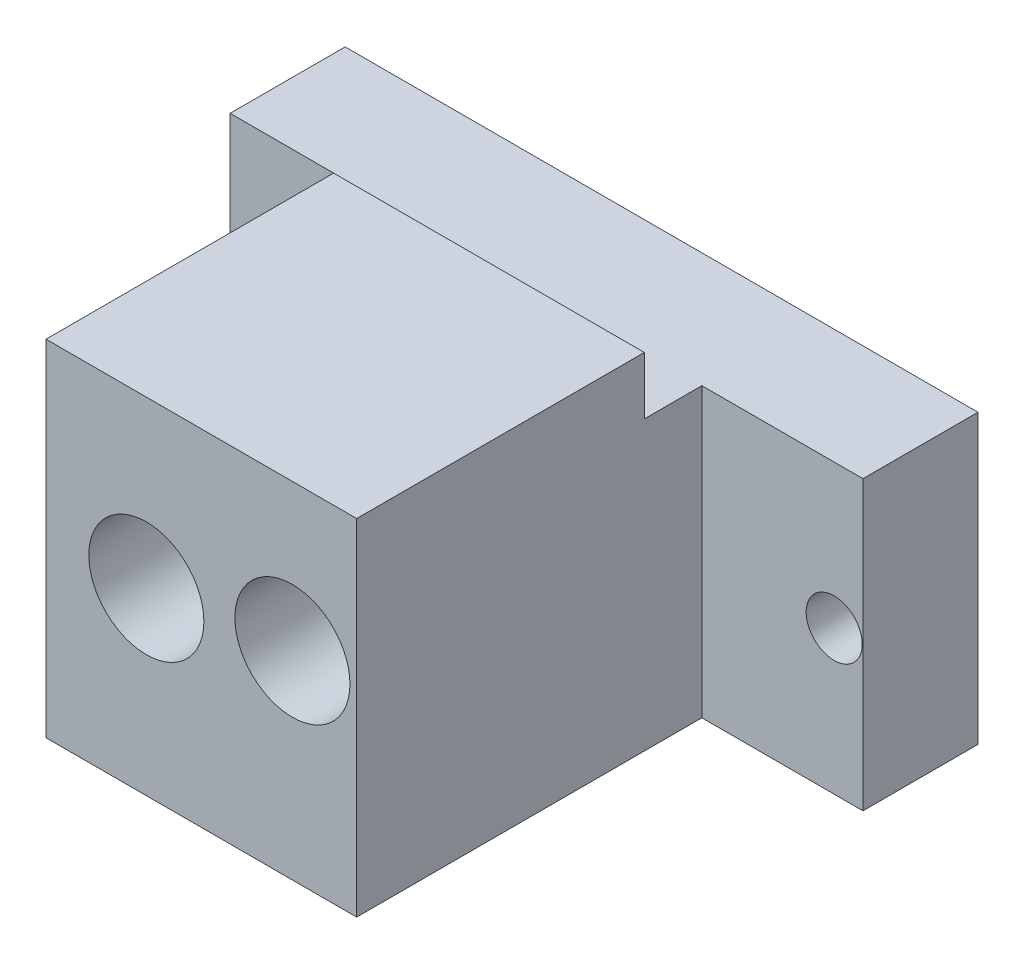
SolidWorks part; units mm, degrees
ref_plane "Front Plane" through (0, 0, 0) normal (0, 0, 1) x (1, 0, 0)
ref_plane "Top Plane" through (0, 0, 0) normal (0, 1, 0) x (1, 0, 0)
ref_plane "Right Plane" through (0, 0, 0) normal (1, 0, 0) x (0, 0, -1)
sketch "Sketch1" plane through (0, 0, 0) normal (0, 0, 1) x (1, 0, 0)
  line L0 (27.5, 25) -> (27.5, 4.2208) construction
  line L1 (0, 0) -> (55, 0)
  line L2 (0, 0) -> (0, 25)
  line L3 (0, 25) -> (55, 25)
  line L4 (55, 0) -> (55, 25)
  circle A0 centre (52.5, 12.5) radius 2.4351
  circle A1 centre (2.5, 12.5) radius 2.4351
  point P7 (27.5, 0)
  point P8 (55, 12.5)
  dimension "D3" = 4.8701
  dimension "D1" = 25
  dimension "D2" = 55
  dimension "D4" = 25
extrude "Boss-Extrude1" add sketch "Sketch1" along normal blind 10
sketch "Sketch2" plane through (0, 0, 10) normal (0, 0, 1) x (1, 0, 0)
  line L0 (55, 25) -> (0, 25) construction
  line L1 (14, 25) -> (41, 25)
  line L2 (14, 25) -> (14, 0)
  line L3 (14, 0) -> (41, 0)
  line L4 (41, 25) -> (41, 0)
  line L5 (0, 0) -> (55, 0) construction
  line L6 (0, 25) -> (0, 0) construction
  line L7 (55, 0) -> (55, 25) construction
  dimension "D1" = 14
  dimension "D2" = 14
extrude "Boss-Extrude2" add sketch "Sketch2" along normal blind 30
sketch "Sketch3" plane through (0, 0, 0) normal (0, -1, 0) x (1, 0, 0)
  line L0 (14, 40) -> (14, 10) construction
  line L1 (41, 40) -> (14, 40)
  line L2 (41, 40) -> (41, 15)
  line L3 (41, 15) -> (14, 15)
  line L4 (14, 40) -> (14, 15)
  dimension "D1" = 25
extrude "Boss-Extrude3" add sketch "Sketch3" against normal blind 30
sketch "Sketch4" plane through (0, 0, 40) normal (0, 0, 1) x (1, 0, 0)
  circle A0 centre (22.7215, 15.6125) radius 5
  circle A1 centre (35.4162, 17.248) radius 5
  dimension "D1" = 10
  dimension "D2" = 10
extrude "Cut-Extrude1" cut sketch "Sketch4" against normal blind 20
